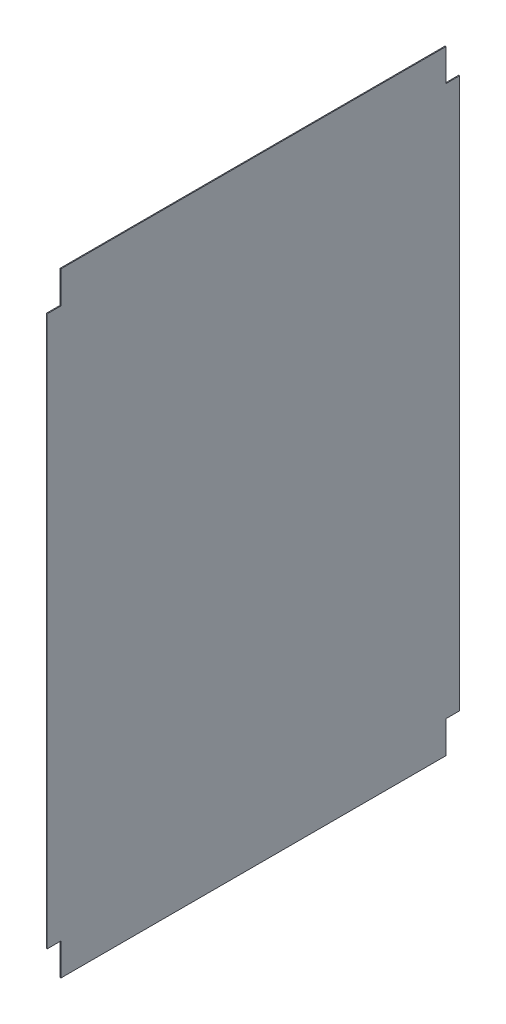
SolidWorks part; units mm, degrees
ref_plane "Front Plane" through (0, 0, 0) normal (0, 0, 1) x (1, 0, 0)
ref_plane "Top Plane" through (0, 0, 0) normal (0, 1, 0) x (1, 0, 0)
ref_plane "Right Plane" through (0, 0, 0) normal (1, 0, 0) x (0, 0, -1)
sketch "Sketch1" plane through (0, 0, 0) normal (1, 0, 0) x (0, 0, -1)
  line L1 (-20.982, 18.1484) -> (24.018, 18.1484)
  line L2 (-20.982, 18.1484) -> (-20.982, -48.8516)
  line L3 (-20.982, -48.8516) -> (24.018, -48.8516)
  line L4 (24.018, 18.1484) -> (24.018, -48.8516)
  dimension "D1" = 45
  dimension "D2" = 67
extrude "Boss-Extrude1" add sketch "Sketch1" along normal blind 0.1
sketch "Sketch3" plane through (0.1, 0, 0) normal (1, 0, 0) x (0, 0, -1)
  line L1 (-20.982, 18.1484) -> (-19.482, 18.1484)
  line L2 (-20.982, 18.1484) -> (-20.982, 14.6484)
  line L3 (-20.982, 14.6484) -> (-19.482, 14.6484)
  line L4 (-19.482, 18.1484) -> (-19.482, 14.6484)
  line L5 (24.018, 18.1484) -> (22.518, 18.1484)
  line L6 (24.018, 18.1484) -> (24.018, 14.6484)
  line L7 (24.018, 14.6484) -> (22.518, 14.6484)
  line L8 (22.518, 18.1484) -> (22.518, 14.6484)
  line L9 (-20.982, -48.8516) -> (-19.482, -48.8516)
  line L10 (-20.982, -48.8516) -> (-20.982, -45.3516)
  line L11 (-20.982, -45.3516) -> (-19.482, -45.3516)
  line L12 (-19.482, -48.8516) -> (-19.482, -45.3516)
  line L13 (24.018, -48.8516) -> (22.518, -48.8516)
  line L14 (24.018, -48.8516) -> (24.018, -45.3516)
  line L15 (24.018, -45.3516) -> (22.518, -45.3516)
  line L16 (22.518, -48.8516) -> (22.518, -45.3516)
  point P20 (-13.3271, -40.422)
  dimension "D1" = 3.5
  dimension "D2" = 1.5
extrude "Cut-Extrude1" cut sketch "Sketch3" against normal blind 0.1
